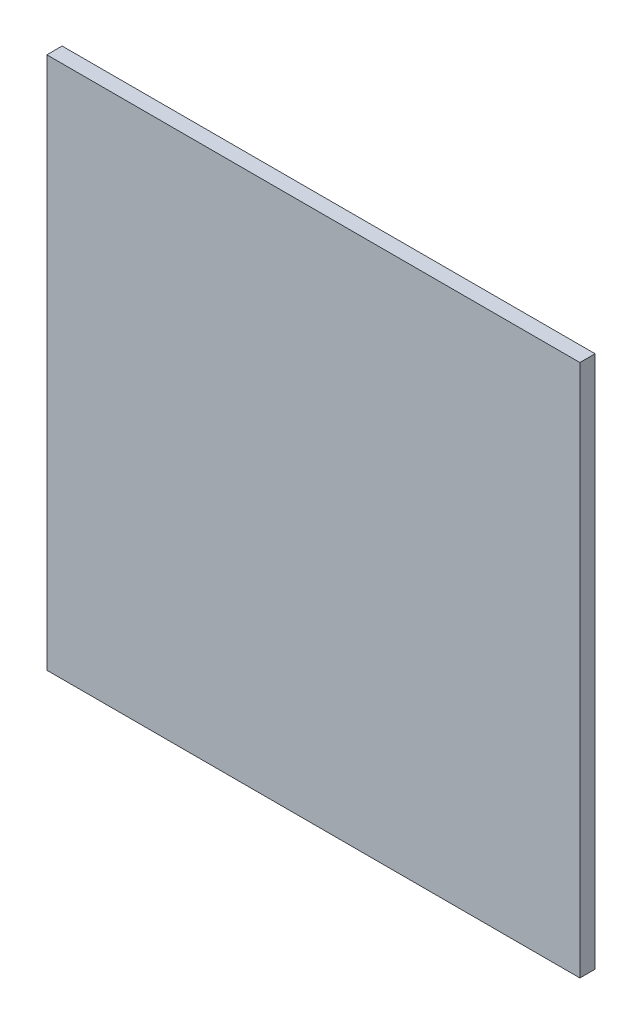
SolidWorks part; units mm, degrees
ref_plane "Plan de face" through (0, 0, 0) normal (0, 0, 1) x (1, 0, 0)
ref_plane "Plan de dessus" through (0, 0, 0) normal (0, 1, 0) x (1, 0, 0)
ref_plane "Plan de droite" through (0, 0, 0) normal (1, 0, 0) x (0, 0, -1)
sketch "Esquisse1" plane through (0, 0, 0) normal (0, 0, 1) x (1, 0, 0)
  line L1 (0, 0) -> (35, 0)
  line L2 (0, 0) -> (0, -35)
  line L3 (0, -35) -> (35, -35)
  line L4 (35, 0) -> (35, -35)
  dimension "D1" = 35
  dimension "D2" = 35
extrude "Boss.-Extru.1" add sketch "Esquisse1" along normal blind 1
sketch "Esquisse2" plane through (0, 0, 0) normal (0, 0, -1) x (-1, 0, 0)
  line L0 (-35, 0) -> (0, 0) construction
  line L1 (-35, -35) -> (-35, 0) construction
  line L2 (0, 0) -> (0, -35) construction
  circle A0 centre (-30, -17.5) radius 1
  circle A1 centre (-5, -17.5) radius 1
  dimension "D4" = 2
  dimension "D1" = 17.5
  dimension "D2" = 5
  dimension "D3" = 5
extrude "Boss.-Extru.2" add sketch "Esquisse2" along normal blind 3
chamfer "Chanfrein1" distance 0.5 angle 45 2 edges at (29, -17.5, -3) (4, -17.5, -3)
